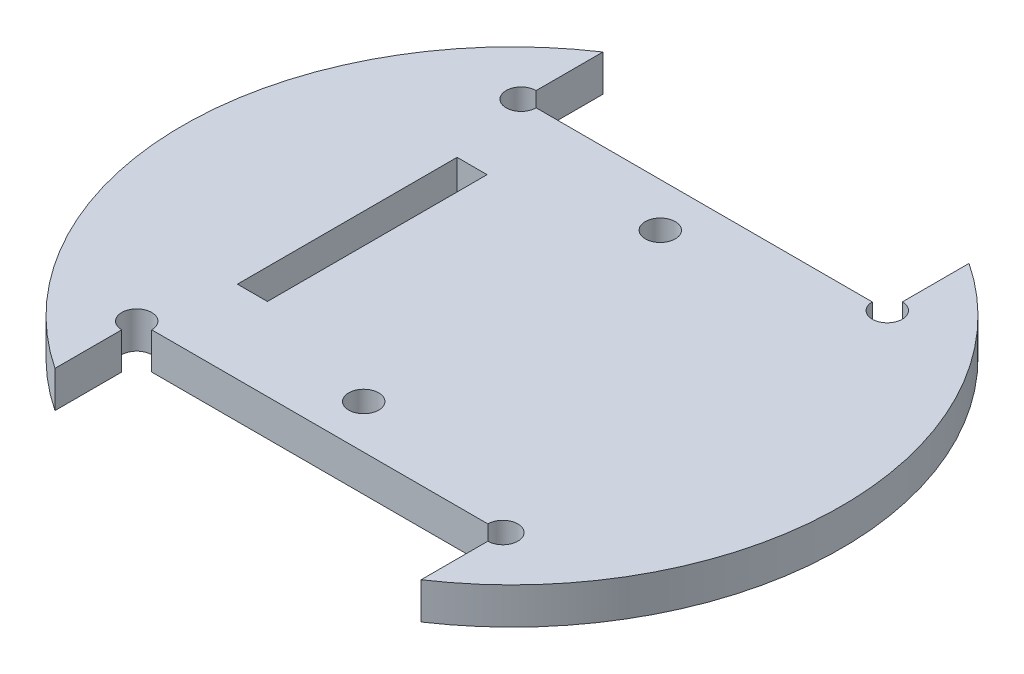
SolidWorks part; units mm, degrees
material "Acrílico (Impacto medio-alto)"
ref_plane "Piano frontale" through (0, 0, 0) normal (0, 0, 1) x (1, 0, 0)
ref_plane "Piano superiore" through (0, 0, 0) normal (0, 1, 0) x (1, 0, 0)
ref_plane "Piano destro" through (0, 0, 0) normal (1, 0, 0) x (0, 0, -1)
sketch "Schizzo1" plane through (0, 0, 0) normal (0, 1, 0) x (1, 0, 0)
  line L0 (-42.1632, 0) -> (43.9871, 0) construction
  line L1 (0, 26.25) -> (0, 0) construction
  line L2 (-25, 37.4166) -> (-25, 26.25)
  line L3 (-25, 26.25) -> (25, 26.25)
  line L4 (25, 37.4166) -> (25, 26.25)
  line L5 (0, 0) -> (0, -26.25) construction
  line L8 (-25, -37.4166) -> (-25, -26.25)
  line L9 (-25, -26.25) -> (25, -26.25)
  line L10 (25, -37.4166) -> (25, -26.25)
  arc A0 (-25, 37.4166) -> (-25, -37.4166) centre (0, 0) ccw
  arc A1 (25, -37.4166) -> (25, 37.4166) centre (0, 0) ccw
  point P3 (0, 45)
  point P8 (0, -45)
  dimension "D1" = 90
  dimension "D2" = 52.5
  dimension "D3" = 25
  dimension "D4" = 25
extrude "Estrusione-Estrusione1" add sketch "Schizzo1" along normal mid plane 5
sketch "Croquis1" plane through (0, -2.5, 0) normal (0, -1, 0) x (1, 0, 0)
  line L0 (-25, 26.25) -> (25, 26.25) construction
  line L1 (-11.5, 26.25) -> (-8.5, 26.25)
  line L2 (-11.5, 26.25) -> (-11.5, 18.25)
  line L3 (-11.5, 18.25) -> (-8.5, 18.25)
  line L4 (-8.5, 26.25) -> (-8.5, 18.25)
  line L5 (8.5, 26.25) -> (11.5, 26.25)
  line L6 (8.5, 26.25) -> (8.5, 18.25)
  line L7 (8.5, 18.25) -> (11.5, 18.25)
  line L8 (11.5, 26.25) -> (11.5, 18.25)
  line L9 (8.5, 31.25) -> (8.5, 27.25) construction
  line L10 (-11.5, 31.25) -> (-11.5, 27.25) construction
  line L11 (11.5, 27.25) -> (11.5, 31.25) construction
  line L12 (-12.75, 15.25) -> (-12.75, 18.25)
  line L13 (-12.75, 15.25) -> (-7.25, 15.25)
  line L14 (-12.75, 18.25) -> (-7.25, 18.25)
  line L15 (-7.25, 15.25) -> (-7.25, 18.25)
  line L16 (-12.75, 15.25) -> (-7.25, 18.25) construction
  line L17 (-12.75, 18.25) -> (-7.25, 15.25) construction
  line L18 (8.6009, 18.25) -> (11.3991, 18.25)
  line L19 (7.25, 15.25) -> (7.25, 18.25)
  line L20 (7.25, 15.25) -> (12.75, 15.25)
  line L21 (7.25, 18.25) -> (12.75, 18.25)
  line L22 (12.75, 15.25) -> (12.75, 18.25)
  line L23 (7.25, 15.25) -> (12.75, 18.25) construction
  line L24 (7.25, 18.25) -> (12.75, 15.25) construction
  line L25 (-45, 0) -> (45, 0) construction
  line L26 (-11.5, 15.25) -> (-8.5, 15.25)
  line L27 (-11.5, 15.25) -> (-11.5, 12.25)
  line L28 (-11.5, 12.25) -> (-8.5, 12.25)
  line L29 (-8.5, 15.25) -> (-8.5, 12.25)
  line L30 (8.5, 15.25) -> (11.5, 15.25)
  line L31 (8.5, 15.25) -> (8.5, 12.25)
  line L32 (8.5, 12.25) -> (11.5, 12.25)
  line L33 (11.5, 15.25) -> (11.5, 12.25)
  line L34 (7.25, -18.25) -> (12.75, -15.25) construction
  line L35 (7.25, -15.25) -> (12.75, -18.25) construction
  line L36 (-12.75, -18.25) -> (-7.25, -15.25) construction
  line L37 (-12.75, -15.25) -> (-7.25, -18.25) construction
  line L38 (11.5, -15.25) -> (11.5, -12.25)
  line L39 (8.5, -12.25) -> (11.5, -12.25)
  line L40 (8.5, -15.25) -> (8.5, -12.25)
  line L41 (8.5, -15.25) -> (11.5, -15.25)
  line L42 (-8.5, -15.25) -> (-8.5, -12.25)
  line L43 (-11.5, -12.25) -> (-8.5, -12.25)
  line L44 (-11.5, -15.25) -> (-11.5, -12.25)
  line L45 (-11.5, -15.25) -> (-8.5, -15.25)
  line L46 (12.75, -15.25) -> (12.75, -18.25)
  line L47 (7.25, -18.25) -> (12.75, -18.25)
  line L48 (7.25, -15.25) -> (12.75, -15.25)
  line L49 (7.25, -15.25) -> (7.25, -18.25)
  line L50 (8.6009, -18.25) -> (11.3991, -18.25)
  line L51 (-7.25, -15.25) -> (-7.25, -18.25)
  line L52 (-12.75, -18.25) -> (-7.25, -18.25)
  line L53 (-12.75, -15.25) -> (-7.25, -15.25)
  line L54 (-12.75, -15.25) -> (-12.75, -18.25)
  line L55 (11.5, -26.25) -> (11.5, -18.25)
  line L56 (8.5, -18.25) -> (11.5, -18.25)
  line L57 (8.5, -26.25) -> (8.5, -18.25)
  line L58 (8.5, -26.25) -> (11.5, -26.25)
  line L59 (-8.5, -26.25) -> (-8.5, -18.25)
  line L60 (-11.5, -18.25) -> (-8.5, -18.25)
  line L61 (-11.5, -26.25) -> (-11.5, -18.25)
  line L62 (-11.5, -26.25) -> (-8.5, -26.25)
  arc A0 (-25, 37.4166) -> (-25, -37.4166) centre (0, 0) ccw construction
  arc A1 (25, -37.4166) -> (25, 37.4166) centre (0, 0) ccw construction
  point P17 (-10, 16.75)
  point P18 (-10, 18.25)
  point P26 (10, 16.75)
  point P27 (10, 18.25)
  point P32 (10, 18.25)
  point P75 (10, -16.75)
  point P76 (-10, -16.75)
  dimension "D1" = 17
  dimension "D2" = 8
  dimension "D3" = 5.5
  dimension "D4" = 3
  dimension "D5" = 5.5
  dimension "D6" = 3
  dimension "D7" = 3
  dimension "D8" = 3
sketch "Croquis2" plane through (0, 2.5, 0) normal (0, 1, 0) x (1, 0, 0)
  line L0 (0, 20.25) -> (0, -20.25) construction
  line L1 (-25, 26.25) -> (-25, -26.25) construction
  circle A14 centre (0, 20.25) radius 2.05
  circle A15 centre (0, -20.25) radius 2.05
  point P2 (-25, 0)
  point P3 (0, 0)
  dimension "D1" = 40.5
  dimension "D2" = 4.1
extrude "Cortar-Extruir1" cut sketch "Croquis2" against normal through all
sketch "Sketch1" plane through (0, 2.5, 0) normal (0, 1, 0) x (1, 0, 0)
  line L0 (0, 26.25) -> (0, -26.25) construction
  line L1 (-22.5, -15) -> (-18.4, -15)
  line L2 (-22.5, -15) -> (-22.5, 15)
  line L3 (-22.5, 15) -> (-18.4, 15)
  line L4 (-18.4, -15) -> (-18.4, 15)
  line L5 (-22.5, -15) -> (-18.4, 15) construction
  line L6 (-22.5, 15) -> (-18.4, -15) construction
  line L7 (25, 26.25) -> (-25, 26.25) construction
  line L8 (-25, -26.25) -> (25, -26.25) construction
  point P0 (-20.45, 0)
  point P5 (0, 0)
  dimension "D1" = 30
  dimension "D2" = 4.1
  dimension "D3" = 18.4
extrude "Cut-Extrude1" cut sketch "Sketch1" against normal up to next
sketch "Sketch2" plane through (0, 2.5, 0) normal (0, 1, 0) x (1, 0, 0)
  circle A0 centre (-25, 26.25) radius 2.05
  circle A1 centre (-25, -26.25) radius 2.05
  circle A2 centre (25, -26.25) radius 2.05
  circle A3 centre (25, 26.25) radius 2.05
  dimension "D1" = 4.1
extrude "Cut-Extrude2" cut sketch "Sketch2" against normal up to next
